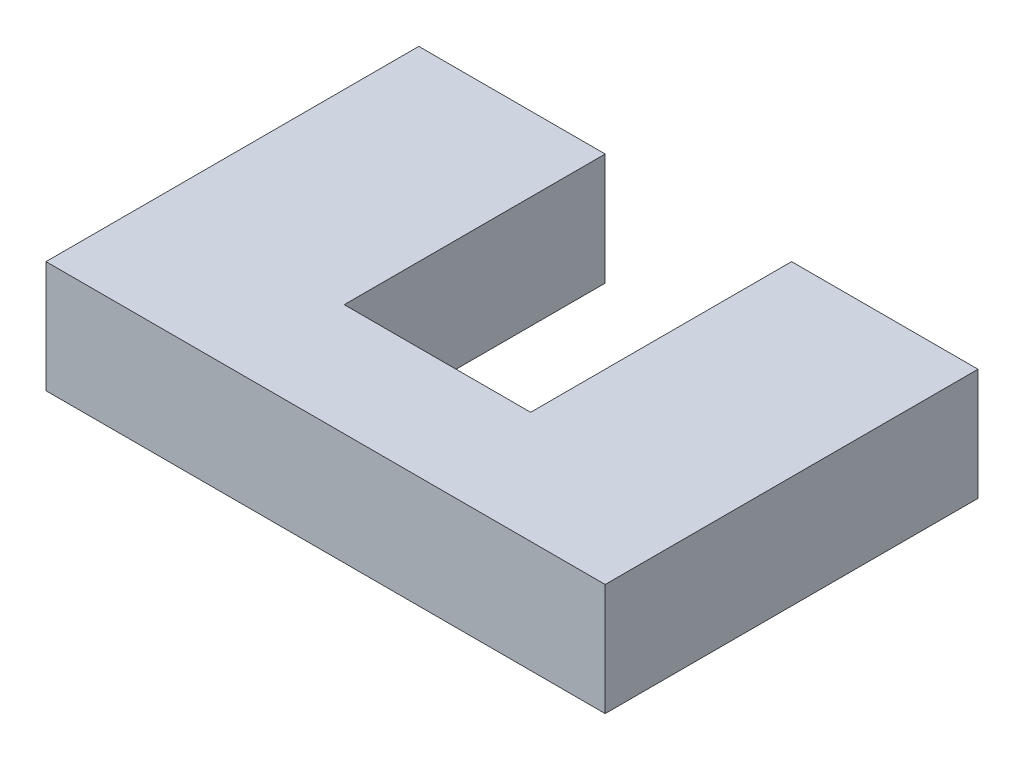
SolidWorks part; units mm, degrees
ref_plane "Front Plane" through (0, 0, 0) normal (0, 0, 1) x (1, 0, 0)
ref_plane "Top Plane" through (0, 0, 0) normal (0, 1, 0) x (1, 0, 0)
ref_plane "Right Plane" through (0, 0, 0) normal (1, 0, 0) x (0, 0, -1)
sketch "Sketch1" plane through (0, 0, 0) normal (0, 1, 0) x (1, 0, 0)
  line L1 (0, 0) -> (3, 0)
  line L2 (0, 0) -> (0, -2)
  line L3 (0, -2) -> (3, -2)
  line L4 (3, 0) -> (3, -2)
  point P4 (0, 0)
  dimension "D1" = 2
  dimension "D2" = 3
extrude "Boss-Extrude1" add sketch "Sketch1" along normal blind 0.6
sketch "Sketch2" plane through (0, 0.6, 0) normal (0, 1, 0) x (1, 0, 0)
  line L0 (3, 0) -> (0, 0) construction
  line L1 (1, 0) -> (2, 0)
  line L2 (1, 0) -> (1, -1.4)
  line L3 (1, -1.4) -> (2, -1.4)
  line L4 (2, 0) -> (2, -1.4)
  point P6 (1.5, 0)
  point P7 (1.5, 0)
  dimension "D1" = 1.4
  dimension "D2" = 1
extrude "Cut-Extrude1" cut sketch "Sketch2" against normal blind 0.6
